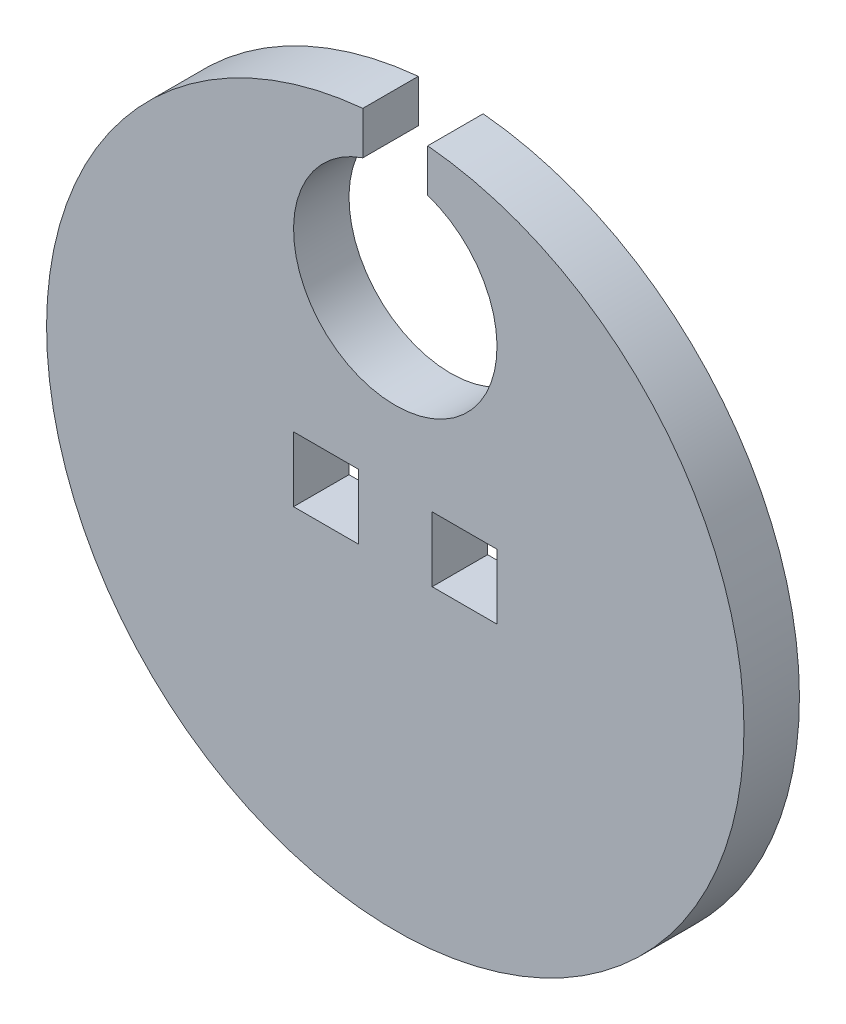
SolidWorks part; units mm, degrees
ref_plane "Front Plane" through (0, 0, 0) normal (0, 0, 1) x (1, 0, 0)
ref_plane "Top Plane" through (0, 0, 0) normal (0, 1, 0) x (1, 0, 0)
ref_plane "Right Plane" through (0, 0, 0) normal (1, 0, 0) x (0, 0, -1)
sketch "Sketch1" plane through (0, 0, 0) normal (0, 0, 1) x (1, 0, 0)
  line L0 (-4.6609, -1.4859) -> (-4.6609, 1.4859)
  line L1 (1.5875, -1.5875) -> (4.7625, -1.5875) construction
  line L2 (1.5875, -1.5875) -> (1.5875, 1.5875) construction
  line L3 (1.5875, 1.5875) -> (4.7625, 1.5875) construction
  line L4 (4.7625, -1.5875) -> (4.7625, 1.5875) construction
  line L5 (1.5875, -1.5875) -> (4.7625, 1.5875) construction
  line L6 (1.5875, 1.5875) -> (4.7625, -1.5875) construction
  line L7 (-4.7625, -1.5875) -> (-1.5875, -1.5875) construction
  line L8 (-4.7625, -1.5875) -> (-4.7625, 1.5875) construction
  line L9 (-4.7625, 1.5875) -> (-1.5875, 1.5875) construction
  line L10 (-1.5875, -1.5875) -> (-1.5875, 1.5875) construction
  line L11 (-4.7625, -1.5875) -> (-1.5875, 1.5875) construction
  line L12 (-4.7625, 1.5875) -> (-1.5875, -1.5875) construction
  line L13 (-4.6609, 1.4859) -> (-1.6891, 1.4859)
  line L14 (-1.6891, -1.4859) -> (-1.6891, 1.4859)
  line L15 (-4.6609, -1.4859) -> (-1.6891, -1.4859)
  line L16 (1.6891, -1.4859) -> (1.6891, 1.4859)
  line L17 (1.6891, 1.4859) -> (4.6609, 1.4859)
  line L18 (4.6609, -1.4859) -> (4.6609, 1.4859)
  line L19 (1.6891, -1.4859) -> (4.6609, -1.4859)
  circle A0 centre (0, 0) radius 15.875 construction
  circle A1 centre (0, 0) radius 15.9766
  point P3 (3.175, 0)
  point P8 (-3.175, 0)
  dimension "D1" = 31.75
  dimension "D2" = 3.175
  dimension "D3" = 3.175
  dimension "D4" = 1.5875
  dimension "D5" = 0.1016
  dimension "D6" = 0.1016
extrude "Boss-Extrude1" add sketch "Sketch1" along normal blind 2.54 contours L1 L4 L3 L2 | L7 L10 L9 L8 | A1 L15 L0 L13 L14 L19 L16 L17 L18 | A0
sketch "Sketch2" plane through (0, 0, 2.54) normal (0, 0, 1) x (1, 0, 0)
  line L0 (-1.5875, 14.0151) -> (-1.5875, 19.05) construction
  line L1 (-1.5875, 19.05) -> (1.5875, 19.05) construction
  line L2 (1.5875, 19.05) -> (1.5875, 14.0151) construction
  line L3 (-1.4859, 13.9427) -> (-1.4859, 18.9484)
  line L4 (-1.4859, 18.9484) -> (1.4859, 18.9484)
  line L5 (1.4859, 18.9484) -> (1.4859, 13.9427)
  arc A0 (-1.5875, 14.0151) -> (1.5875, 14.0151) centre (0, 9.525) ccw construction
  circle A1 centre (0, 9.525) radius 1.5875 construction
  arc A2 (-1.4859, 13.9427) -> (1.4859, 13.9427) centre (0, 9.525) ccw
  dimension "D1" = 9.525
  dimension "D3" = 3.175
  dimension "D2" = 9.525
  dimension "D4" = 9.525
  dimension "D5" = 0.1016
extrude "Cut-Extrude1" cut sketch "Sketch2" against normal blind 2.54
